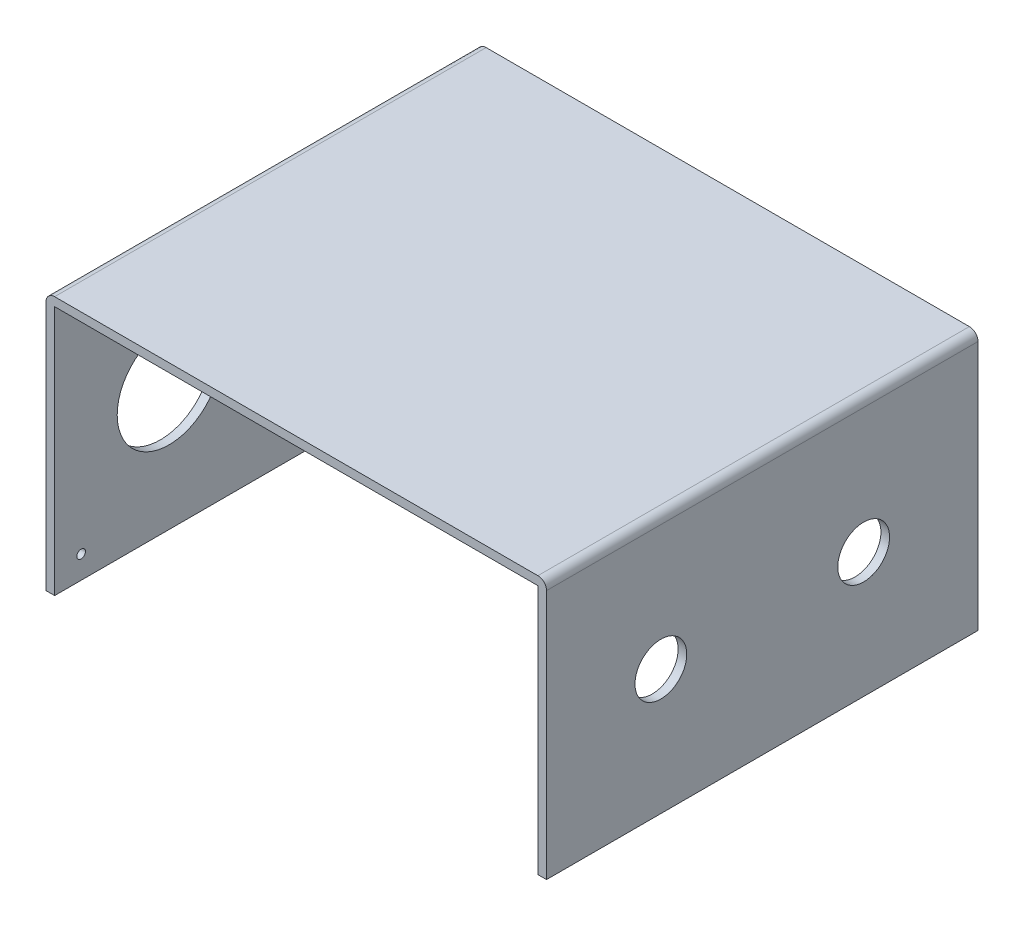
SolidWorks part; units mm, degrees
material "3003 Alaşım"
ref_plane "Ön Düzlem" through (0, 0, 0) normal (0, 0, 1) x (1, 0, 0)
ref_plane "Üst Düzlem" through (0, 0, 0) normal (0, 1, 0) x (1, 0, 0)
ref_plane "Sağ Düzlem" through (0, 0, 0) normal (1, 0, 0) x (0, 0, -1)
sketch "Çizim1" plane through (0, 0, 0) normal (0, 0, 1) x (1, 0, 0)
  line L0 (0, 0) -> (0, 29)
  line L1 (1, 30) -> (57, 30)
  line L2 (58, 29) -> (58, 0)
  arc A0 (0, 29) -> (1, 30) centre (1, 29) cw
  arc A1 (57, 30) -> (58, 29) centre (57, 29) cw
  point P7 (0, 30)
  point P10 (58, 30)
  dimension "D3" = 1
  dimension "D1" = 58
  dimension "D2" = 30
extrude "Ekstrüzyon-İnce1" add sketch "Çizim1" along normal blind 50 thin
sketch "Çizim2" plane through (58, 0, 0) normal (1, 0, 0) x (0, 0, -1)
  line L0 (-50, 14.5) -> (0, 14.5) construction
  line L1 (-50, 29) -> (-50, 0) construction
  line L2 (0, 29) -> (0, 0) construction
  line L3 (-25, 25.8154) -> (-25, 3.1846) construction
  line L4 (-36.75, 25.8154) -> (-36.75, 3.1846) construction
  line L5 (-13.25, 25.8154) -> (-13.25, 3.1846) construction
  circle A0 centre (-36.75, 14.5) radius 3
  circle A1 centre (-13.25, 14.5) radius 3
  point P9 (-25, 14.5)
  dimension "D1" = 11.75
  dimension "D2" = 11.75
extrude "Kes-Ekstrüzyon1" cut sketch "Çizim2" against normal blind 78
sketch "Çizim3" plane through (0, 0, 0) normal (-1, 0, 0) x (0, 0, 1)
  circle A0 centre (46.9263, 2.6362) radius 0.5
extrude "Kes-Ekstrüzyon2" cut sketch "Çizim3" against normal blind 22
sketch "Çizim4" plane through (0, 0, 0) normal (-1, 0, 0) x (0, 0, 1)
  circle A0 centre (36.75, 14.5) radius 6
extrude "Kes-Ekstrüzyon3" cut sketch "Çizim4" against normal blind 22
